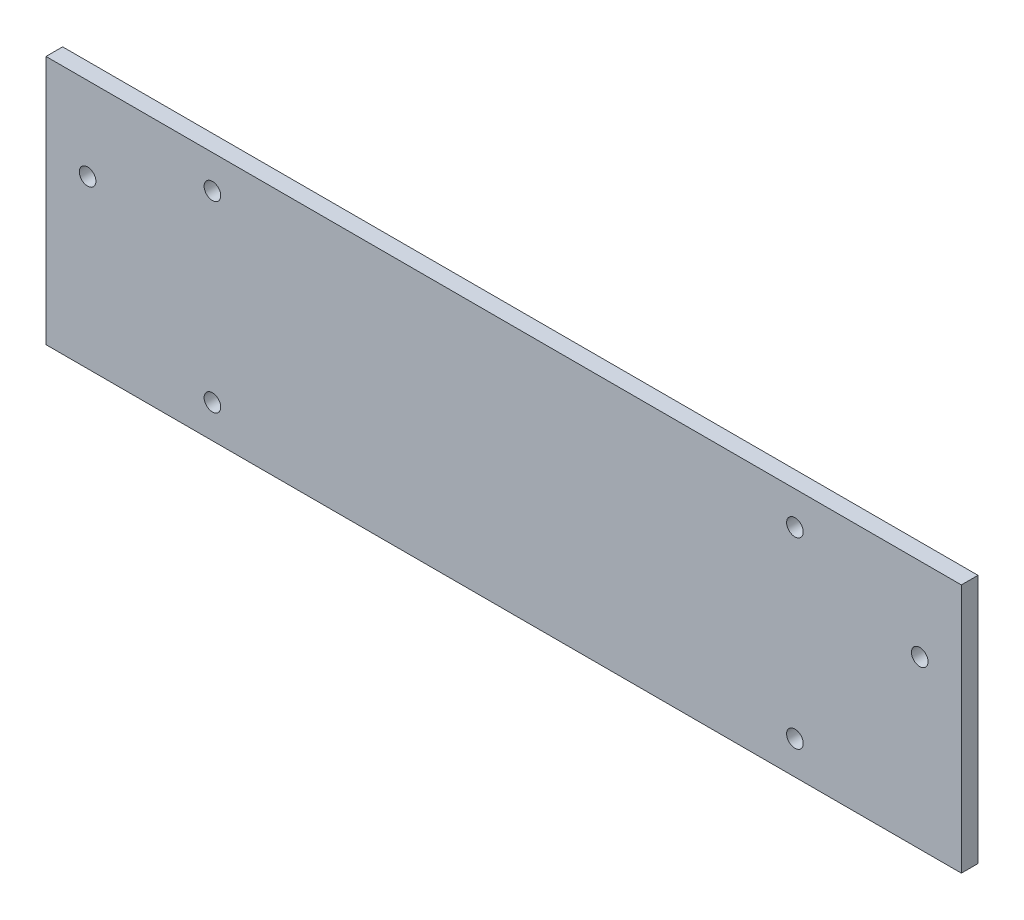
SolidWorks part; units mm, degrees
ref_plane "Front Plane" through (0, 0, 0) normal (0, 0, 1) x (1, 0, 0)
ref_plane "Top Plane" through (0, 0, 0) normal (0, 1, 0) x (1, 0, 0)
ref_plane "Right Plane" through (0, 0, 0) normal (1, 0, 0) x (0, 0, -1)
sketch "Sketch1" plane through (0, 0, 0) normal (0, 0, 1) x (1, 0, 0)
  line L1 (-167.64, 22.3288) -> (111.76, 22.3288)
  line L2 (-167.64, 22.3288) -> (-167.64, -53.8712)
  line L3 (-167.64, -53.8712) -> (111.76, -53.8712)
  line L4 (111.76, 22.3288) -> (111.76, -53.8712)
  dimension "D1" = 279.4
  dimension "D2" = 76.2
extrude "Boss-Extrude1" add sketch "Sketch1" along normal blind 5.08
sketch "Sketch2" plane through (0, 0, 5.08) normal (0, 0, 1) x (1, 0, 0)
  line L0 (-116.84, 12.1688) -> (60.96, 12.1688) construction
  line L1 (60.96, 12.1688) -> (60.96, -43.7112) construction
  line L2 (60.96, -43.7112) -> (-116.84, -43.7112) construction
  line L3 (-116.84, -43.7112) -> (-116.84, 12.1688) construction
  line L4 (-167.64, 22.3288) -> (-167.64, -53.8712) construction
  line L5 (111.76, -53.8712) -> (111.76, 22.3288) construction
  line L6 (111.76, 22.3288) -> (-167.64, 22.3288) construction
  line L7 (-167.64, -53.8712) -> (111.76, -53.8712) construction
  circle A0 centre (-154.94, -3.0712) radius 2.54
  circle A1 centre (-116.84, 12.1688) radius 2.54
  circle A2 centre (-116.84, -43.7112) radius 2.54
  circle A3 centre (60.96, -43.7112) radius 2.54
  circle A4 centre (60.96, 12.1688) radius 2.54
  circle A5 centre (99.06, -3.0712) radius 2.54
  dimension "D7" = 5.08
  dimension "D8" = 5.08
  dimension "D9" = 5.08
  dimension "D10" = 5.08
  dimension "D11" = 5.08
  dimension "D12" = 5.08
  dimension "D13" = 50.8
  dimension "D1" = 50.8
  dimension "D2" = 50.8
  dimension "D3" = 10.16
  dimension "D4" = 10.16
  dimension "D5" = 50.8
  dimension "D6" = 12.7
  dimension "D14" = 12.7
extrude "Cut-Extrude1" cut sketch "Sketch2" against normal blind 12.7
sketch "Sketch3" [suppressed] plane through (0, 0, 5.08) normal (0, 0, 1) x (1, 0, 0)
  line L0 (-167.64, -53.8712) -> (111.76, -53.8712) construction
  line L1 (-167.64, 22.3288) -> (-167.64, -53.8712) construction
  circle A0 centre (-66.04, -28.4712) radius 12.7
  dimension "D1" = 25.4
  dimension "D2" = 25.4
  dimension "D3" = 101.6
extrude "Cut-Extrude2" [suppressed] cut sketch "Sketch3" against normal blind 25.4
sketch "Sketch4" [suppressed] plane through (0, 0, 5.08) normal (0, 0, 1) x (1, 0, 0)
  line L0 (-167.64, -53.8712) -> (111.76, -53.8712) construction
  line L1 (-167.64, 22.3288) -> (-167.64, -53.8712) construction
  text T0 "The Holy Turret of Antioch"
  dimension "D1" = 38.1
  dimension "D2" = 101.6
extrude "Cut-Extrude7" [suppressed] cut sketch "Sketch4" against normal blind 25.4
